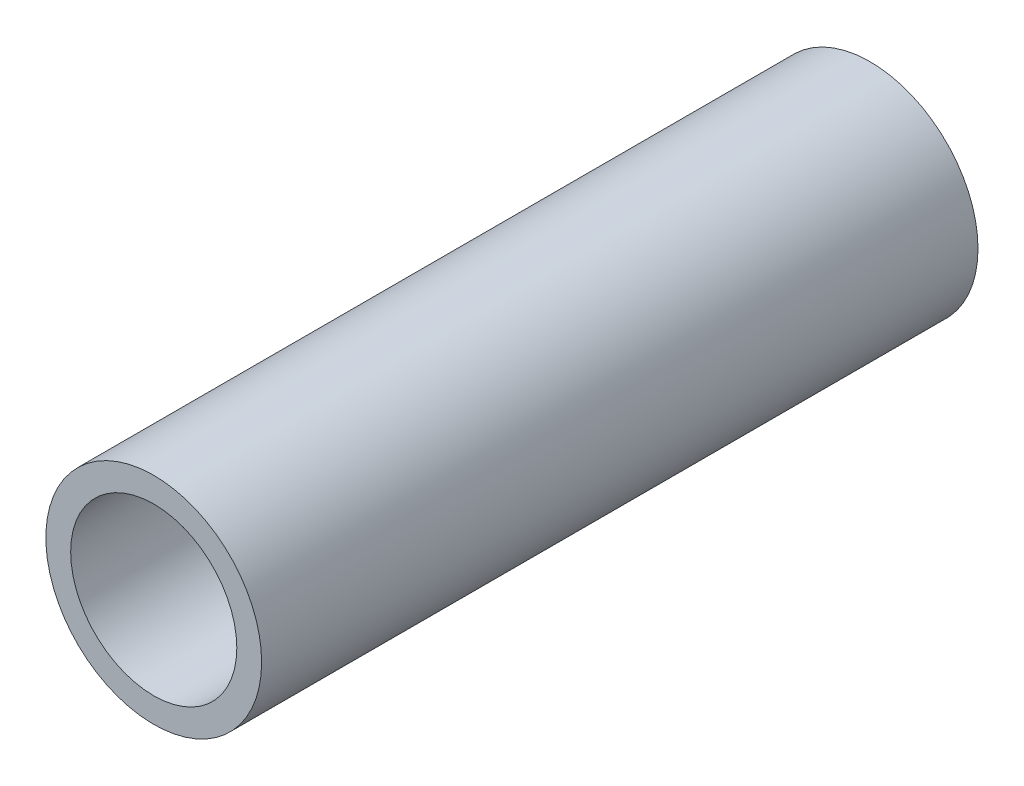
SolidWorks part; units mm, degrees
material "Delrin 2700 NC010, Low Viscosity Acetal Copolymer (SS)"
ref_plane "Front" through (0, 0, 0) normal (0, 0, 1) x (1, 0, 0)
ref_plane "Top" through (0, 0, 0) normal (0, 1, 0) x (1, 0, 0)
ref_plane "Right" through (0, 0, 0) normal (1, 0, 0) x (0, 0, -1)
sketch "Sketch1" plane through (0, 0, 0) normal (0, 0, 1) x (1, 0, 0)
  circle A0 centre (0, 0) radius 4.8895
  circle A1 centre (0, 0) radius 6.35
  dimension "D1" = 9.779
  dimension "D2" = 12.7
extrude "Boss-Extrude1" add sketch "Sketch1" along normal blind 42.164
